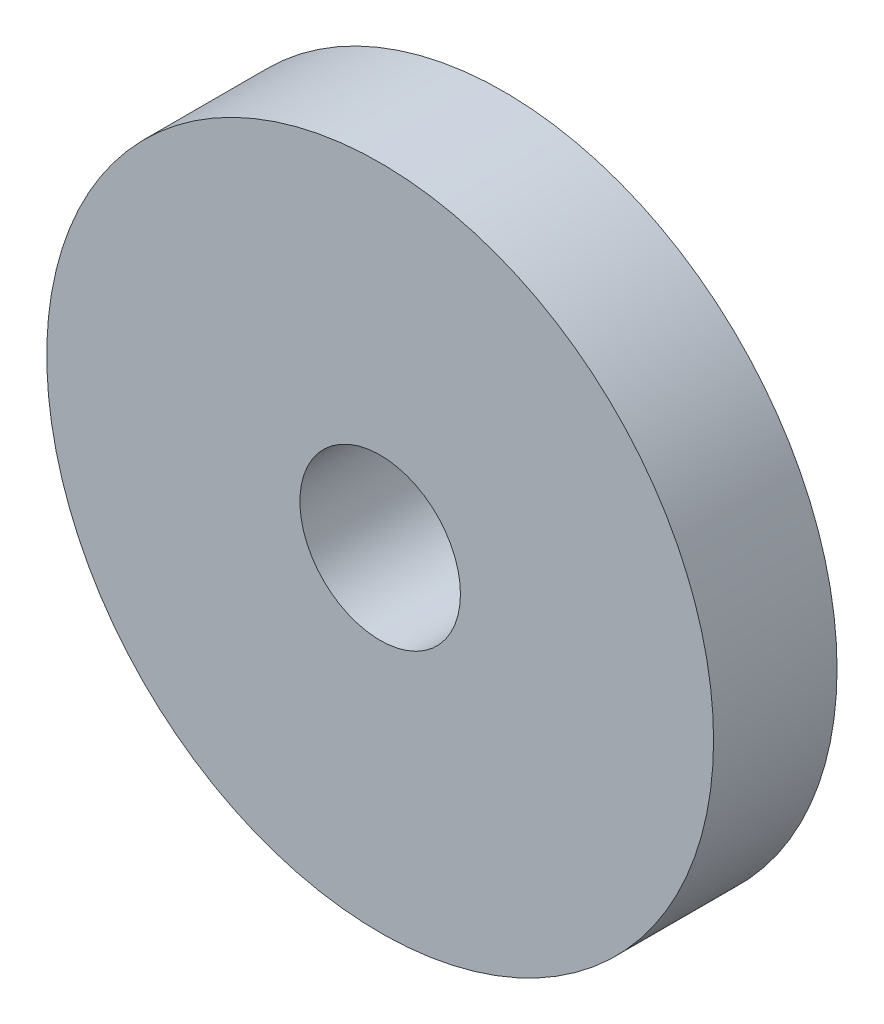
SolidWorks part; units mm, degrees
material "Zinc AC41A Alloy, As Cast"
ref_plane "Front Plane" through (0, 0, 0) normal (0, 0, 1) x (1, 0, 0)
ref_plane "Top Plane" through (0, 0, 0) normal (0, 1, 0) x (1, 0, 0)
ref_plane "Right Plane" through (0, 0, 0) normal (1, 0, 0) x (0, 0, -1)
sketch "Sketch1" plane through (0, 0, 0) normal (0, 0, 1) x (1, 0, 0)
  circle A0 centre (0, 0) radius 54
  dimension "D1" = 108
extrude "Boss-Extrude1" add sketch "Sketch1" along normal blind 20
sketch "Sketch2" plane through (0, 0, 20) normal (0, 0, 1) x (1, 0, 0)
  circle A0 centre (0, 0) radius 13
  dimension "D1" = 26
extrude "Cut-Extrude1" cut sketch "Sketch2" against normal up to next
